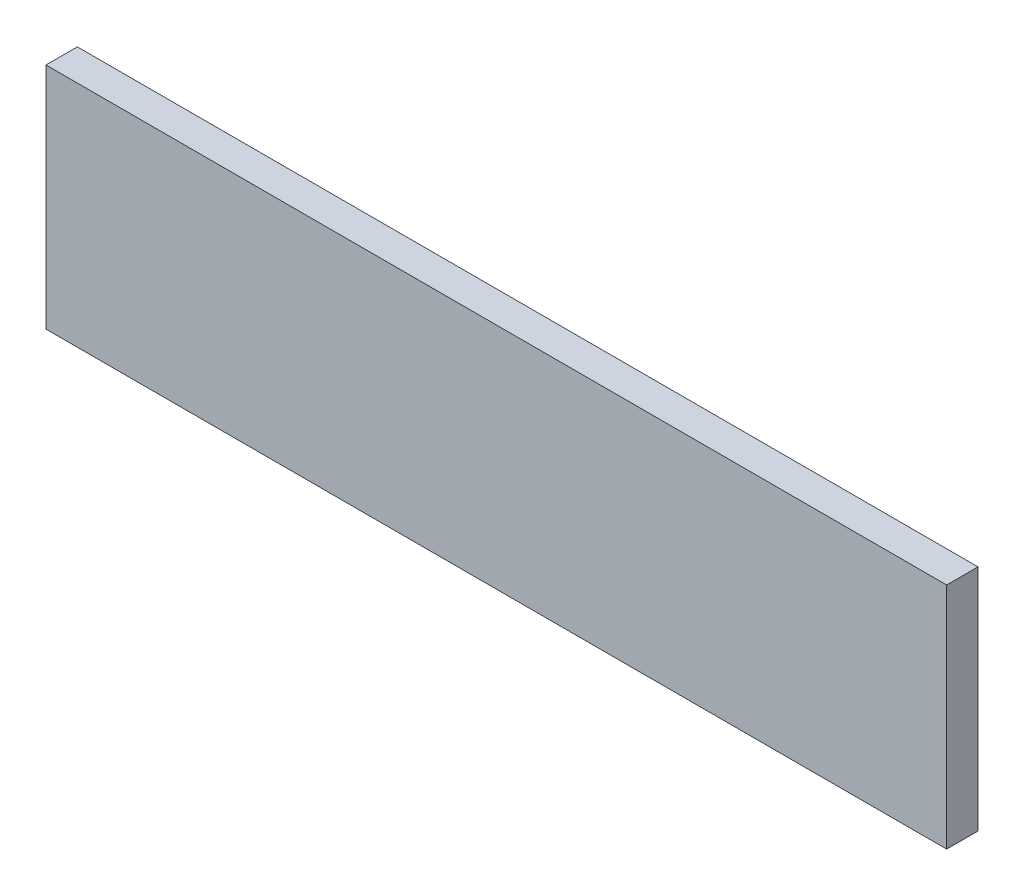
SolidWorks part; units mm, degrees
material "PVC Rigid"
ref_plane "Front" through (0, 0, 0) normal (0, 0, 1) x (1, 0, 0)
ref_plane "Top" through (0, 0, 0) normal (0, 1, 0) x (1, 0, 0)
ref_plane "Right" through (0, 0, 0) normal (1, 0, 0) x (0, 0, -1)
sketch "Sketch1" plane through (0, 0, 0) normal (0, 0, 1) x (1, 0, 0)
  line L0 (26.15, 0) -> (-260.15, 0) construction
  line L1 (19.8, 0) -> (-253.8, 0)
  line L2 (19.8, 0) -> (19.8, 69.5)
  line L3 (19.8, 69.5) -> (-253.8, 69.5)
  line L4 (-253.8, 0) -> (-253.8, 69.5)
  point P9 (-117, 0)
extrude "Boss-Extrude1" add sketch "Sketch1" against normal blind 9.525
